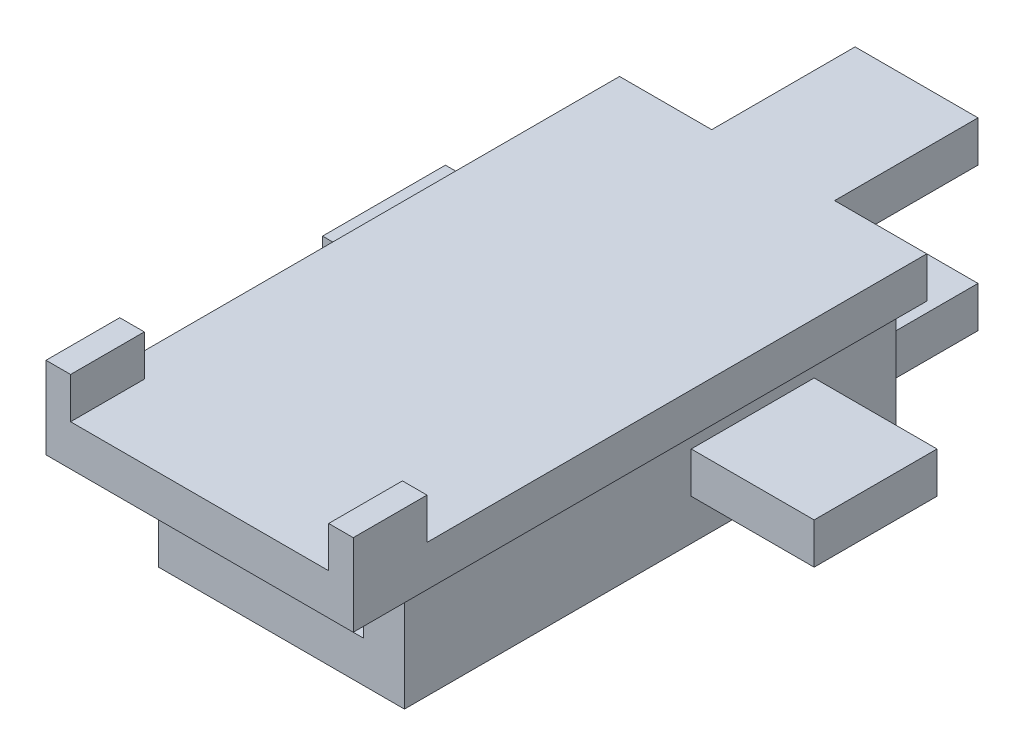
SolidWorks part; units mm, degrees
ref_plane "Front Plane" through (0, 0, 0) normal (0, 0, 1) x (1, 0, 0)
ref_plane "Top Plane" through (0, 0, 0) normal (0, 1, 0) x (1, 0, 0)
ref_plane "Right Plane" through (0, 0, 0) normal (1, 0, 0) x (0, 0, -1)
sketch "Sketch1" plane through (0, 0, 0) normal (0, 1, 0) x (1, 0, 0)
  line L1 (-3.75, -5) -> (3.75, -5)
  line L2 (-3.75, -5) -> (-3.75, 5)
  line L3 (-3.75, 5) -> (3.75, 5)
  line L4 (3.75, -5) -> (3.75, 5)
  line L5 (0, 5) -> (0, -5) construction
  line L6 (-3.75, 0) -> (3.75, 0) construction
  point P0 (0, 0)
  dimension "D1" = 10
  dimension "D2" = 7.5
extrude "Boss-Extrude1" add sketch "Sketch1" along normal blind 1
ref_plane "Plane1" through (0, 3.5, 0) normal (0, 1, 0) x (1, 0, 0)
sketch "Sketch10" plane through (0, 0, 5) normal (0, 0, 1) x (1, 0, 0)
  line L1 (-3.75, 1) -> (3.75, 1)
  line L2 (-3.75, 1) -> (-3.75, 0)
  line L3 (-3.75, 0) -> (3.75, 0)
  line L4 (3.75, 1) -> (3.75, 0)
extrude "Boss-Extrude5" add sketch "Sketch10" along normal blind 2
sketch "Sketch56" plane through (0, 0, 7) normal (0, 0, 1) x (1, 0, 0)
  line L1 (-3.75, 1) -> (3.75, 1)
  line L2 (-3.75, 1) -> (-3.75, 0)
  line L3 (-3.75, 0) -> (3.75, 0)
  line L4 (3.75, 1) -> (3.75, 0)
extrude "Boss-Extrude17" add sketch "Sketch56" along normal blind 2
sketch "Sketch57" plane through (0, 0, -5) normal (0, 0, -1) x (-1, 0, 0)
  line L0 (0, 0) -> (0, 1) construction
  line L1 (-3.75, 1) -> (3.75, 1) construction
  line L3 (-1.5, 0) -> (1.5, 0)
  line L4 (-1.5, 0) -> (-1.5, 1)
  line L5 (-1.5, 1) -> (1.5, 1)
  line L6 (1.5, 0) -> (1.5, 1)
  line L7 (-1.5, 0) -> (1.5, 1) construction
  line L8 (-1.5, 1) -> (1.5, 0) construction
  point P5 (0, 0.5)
  dimension "D1" = 3
extrude "Boss-Extrude18" add sketch "Sketch57" along normal blind 5
sketch "Sketch58" plane through (1.5, 0, 0) normal (1, 0, 0) x (0, 0, -1)
  line L0 (10, 1) -> (5, 1) construction
  line L1 (10, 0) -> (8.5, 0)
  line L2 (10, 0) -> (10, 1)
  line L3 (10, 1) -> (8.5, 1)
  line L4 (8.5, 0) -> (8.5, 1)
  dimension "D1" = 1.5
extrude "Boss-Extrude19" add sketch "Sketch58" along normal blind 2
sketch "Sketch59" plane through (-1.5, 0, 0) normal (-1, 0, 0) x (0, 0, 1)
  line L0 (-10, 1) -> (-5, 1) construction
  line L1 (-10, 0) -> (-8.5, 0)
  line L2 (-10, 0) -> (-10, 1)
  line L3 (-10, 1) -> (-8.5, 1)
  line L4 (-8.5, 0) -> (-8.5, 1)
  dimension "D1" = 1.5
extrude "Boss-Extrude20" add sketch "Sketch59" along normal blind 2
sketch "Sketch60" plane through (0, 1, 0) normal (0, 1, 0) x (1, 0, 0)
  line L0 (3.5, 9.25) -> (2.5, 9.25) construction
  line L1 (3.5, 10) -> (3.5, 8.5) construction
  line L2 (3.5, 8.5) -> (1.5, 8.5) construction
  line L3 (2.5, 8.75) -> (2.5, 9.75)
  line L4 (0, 10) -> (0, 9.0116) construction
  line L5 (2.5, 8.5) -> (3.5, 8.5)
  line L6 (2.5, 8.5) -> (2.5, 10)
  line L7 (2.5, 10) -> (3.5, 10)
  line L8 (3.5, 8.5) -> (3.5, 10)
  line L9 (-3.5, 10) -> (3.5, 10) construction
  line L10 (2.5, 8.5) -> (3.5, 8.5)
  line L11 (2.5, 10) -> (3.5, 10)
  line L12 (-3.5, 9.25) -> (-2.5, 9.25) construction
  line L13 (-2.5, 10) -> (-3.5, 10)
  line L14 (-2.5, 8.5) -> (-3.5, 8.5)
  line L15 (-3.5, 8.5) -> (-3.5, 10)
  line L16 (-2.5, 10) -> (-3.5, 10)
  line L17 (-2.5, 8.5) -> (-2.5, 10)
  line L18 (-2.5, 8.5) -> (-3.5, 8.5)
  line L19 (-2.5, 8.75) -> (-2.5, 9.75)
  point P10 (2.5, 9.25)
  dimension "D1" = 1
extrude "Boss-Extrude23" add sketch "Sketch60" along normal blind 1.5 contours L8 L17 L6 L7 | L6 L4 L5 L3
sketch "Sketch61" plane through (0, 2.5, 0) normal (0, 1, 0) x (1, 0, 0)
  line L0 (2.5, 8.8704) -> (2.5, 9.6204)
  line L1 (-3.5, 10) -> (-3.5, 8.5) construction
  line L3 (-3.5, 8.8704) -> (-3.5, 9.6204)
  line L4 (-2.5, 8.5) -> (-2.5, 10) construction
  line L5 (-3.5, 8.8704) -> (-2.5, 8.8704)
  line L6 (-3.5, 8.8704) -> (-3.5, 9.6204)
  line L7 (-3.5, 9.6204) -> (-2.5, 9.6204)
  line L8 (-2.5, 8.8704) -> (-2.5, 9.6204)
  line L9 (0, 10) -> (0, 8.8704) construction
  line L10 (-2.5, 10) -> (2.5, 10) construction
  line L11 (3.5, 9.6204) -> (2.5, 9.6204)
  line L12 (3.5, 8.8704) -> (3.5, 9.6204)
  line L13 (3.5, 8.8704) -> (2.5, 8.8704)
  line L14 (3.5, 8.8704) -> (3.5, 9.6204)
  point P9 (-3.5, 9.2454)
  point P18 (3.5, 9.2454)
  line M3 (2.5, 10) -> (2.5, 8.5)
  line M5 (3.5, 8.5) -> (3.5, 10)
  dimension "D1" = 0.75
extrude "Cut-Extrude1" cut sketch "Sketch61" against normal blind 0.5 contours L5 L8 L7 L3 | L13 L11 M5 M3
sketch "Sketch62" plane through (0, 0, 0) normal (0, -1, 0) x (-1, 0, 0)
  line L0 (-1.5, 5) -> (1.5, 5)
  line L1 (0, 5) -> (0, -7) construction
  line L2 (3, -7) -> (-3, -7)
  line L3 (-3.75, 5) -> (-1.5, 5) construction
  line L4 (3, -7) -> (-3, -7)
  line L5 (3, -7) -> (3, 5)
  line L6 (3, 5) -> (-3, 5)
  line L7 (-3, -7) -> (-3, 5)
  point P10 (0, -7)
  line M5 (3.75, 5) -> (1.5, 5)
  line M13 (-1.5, 5) -> (-3.75, 5)
  dimension "D1" = 12
extrude "Boss-Extrude25" add sketch "Sketch62" along normal blind 3 contours L6 L1 L2 L5 M5 | L1 L0 L7 L4 M13
sketch "Sketch64" plane through (0, 0, 7) normal (0, 0, 1) x (1, 0, 0)
  line L0 (-2, 0) -> (2, 0)
  line L2 (-3.75, 0) -> (3.75, 0) construction
  line L4 (-2, 0) -> (2, 0)
  line L5 (-2, 0) -> (-2, -2)
  line L6 (-2, -2) -> (2, -2)
  line L7 (2, 0) -> (2, -2)
  point P7 (0, 0)
  line M2 (3, 0) -> (-3, 0)
  dimension "D1" = 2
extrude "Cut-Extrude2" cut sketch "Sketch64" against normal up to surface (12 mm away) contours L7 L5 L6 M2 up to face at (0, -0.1667, -5)
sketch "Sketch65" plane through (0, 0, -5) normal (0, 0, -1) x (-1, 0, 0)
  line L0 (-3, -3) -> (3, -3) construction
  line L1 (-2, -2) -> (2, -2)
  line L2 (-2, -2) -> (-2, -3)
  line L3 (-2, -3) -> (2, -3)
  line L4 (2, -2) -> (2, -3)
  dimension "D1" = 4
extrude "Boss-Extrude26" add sketch "Sketch65" along normal blind 3
sketch "Sketch66" plane through (0, -3, 0) normal (0, -1, 0) x (-1, 0, 0)
  line L0 (0, -7) -> (0, -5) construction
  line L1 (0, -5) -> (0, 5) construction
  line L2 (3, -7) -> (-3, -7) construction
  circle A0 centre (0, -5) radius 1
  circle A1 centre (0, 5) radius 1
  dimension "D2" = 10
  dimension "D1" = 2
extrude "Cut-Extrude3" cut sketch "Sketch66" against normal up to surface (1 mm away) up to face at (0, -2, -2)
sketch "Sketch67" plane through (-3, 0, 0) normal (-1, 0, 0) x (0, 0, 1)
  line L0 (-5, 0) -> (-3, 0)
  line L1 (-5, 0) -> (9, 0) construction
  line L2 (-3, 0) -> (-3, -1)
  line L3 (-5, -3) -> (-5, 0) construction
  line L4 (-3, -1) -> (0, -1)
  line L5 (-3, -1) -> (-3, -2)
  line L6 (-3, -2) -> (0, -2)
  line L7 (0, -1) -> (0, -2)
  line L8 (-5, -1) -> (6, -1)
  line L9 (-5, -1) -> (-5, -2)
  line L10 (-5, -2) -> (6, -2)
  line L11 (6, -1) -> (6, -2)
  dimension "D1" = 2
  dimension "D2" = 1
  dimension "D3" = 1
  dimension "D4" = 3
  dimension "D5" = 11
sketch "Sketch68" plane through (3, 0, 0) normal (1, 0, 0) x (0, 0, -1)
  line L0 (5, 0) -> (3, 0)
  line L1 (-9, 0) -> (5, 0) construction
  line L2 (3, 0) -> (3, -1)
  line L3 (5, -3) -> (5, 0) construction
  line L4 (3, -1) -> (0, -1)
  line L5 (3, -1) -> (3, -2)
  line L6 (3, -2) -> (0, -2)
  line L7 (0, -1) -> (0, -2)
  line L8 (5, -2) -> (-6, -2)
  line L9 (5, -2) -> (5, -1)
  line L10 (5, -1) -> (-6, -1)
  line L11 (-6, -2) -> (-6, -1)
  dimension "D1" = 2
  dimension "D2" = 1
  dimension "D3" = 3
  dimension "D4" = 1
  dimension "D5" = 11
sketch "Sketch69" plane through (0, 0, 0) normal (0, -1, 0) x (1, 0, 0)
  line L0 (3.5, -8.5) -> (3.5, -10) construction
  line L1 (-3.5, -8.5) -> (3.5, -8.5)
  line L2 (-3.5, -8.5) -> (-3.5, -10)
  line L3 (-3.5, -10) -> (3.5, -10)
  line L4 (3.5, -8.5) -> (3.5, -10)
  line L5 (3.5, -10) -> (-3.5, -10) construction
extrude "Cut-Extrude8" cut sketch "Sketch69" against normal blind 10
sketch "Sketch70" plane through (0, 1, 0) normal (0, 1, 0) x (1, 0, 0)
  line L0 (-2.625, 5) -> (-2.625, -7.2) construction
  line L1 (-1.5, 5) -> (-3.75, 5) construction
  line L2 (-3.75, -7.2) -> (-3.15, -7.2) construction
  line L3 (-3.75, 5) -> (-3.75, -9) construction
  line L4 (0, -9) -> (0, -8.2959) construction
  line L5 (3.75, -7.2) -> (3.15, -7.2) construction
  line L6 (3.75, -9) -> (-3.75, -9) construction
  line L7 (-3.75, -7.2) -> (-3.15, -7.2)
  line L8 (-3.75, -7.2) -> (-3.75, -9)
  line L9 (-3.75, -9) -> (-3.15, -9)
  line L10 (-3.15, -7.2) -> (-3.15, -9)
  line L11 (3.15, -7.2) -> (3.15, -9)
  line L12 (3.75, -9) -> (3.15, -9)
  line L13 (3.75, -7.2) -> (3.75, -9)
  line L14 (3.75, -7.2) -> (3.15, -7.2)
  dimension "D1" = 12.2
  dimension "D2" = 0.6
  dimension "D3" = 1.8
extrude "Boss-Extrude27" add sketch "Sketch70" along normal blind 1
extrude "Boss-Extrude28" add sketch "Sketch68" along normal blind 3 contours L5 L6 L7 L4
extrude "Boss-Extrude29" add sketch "Sketch67" along normal blind 3 contours L5 L6 L7 L4
